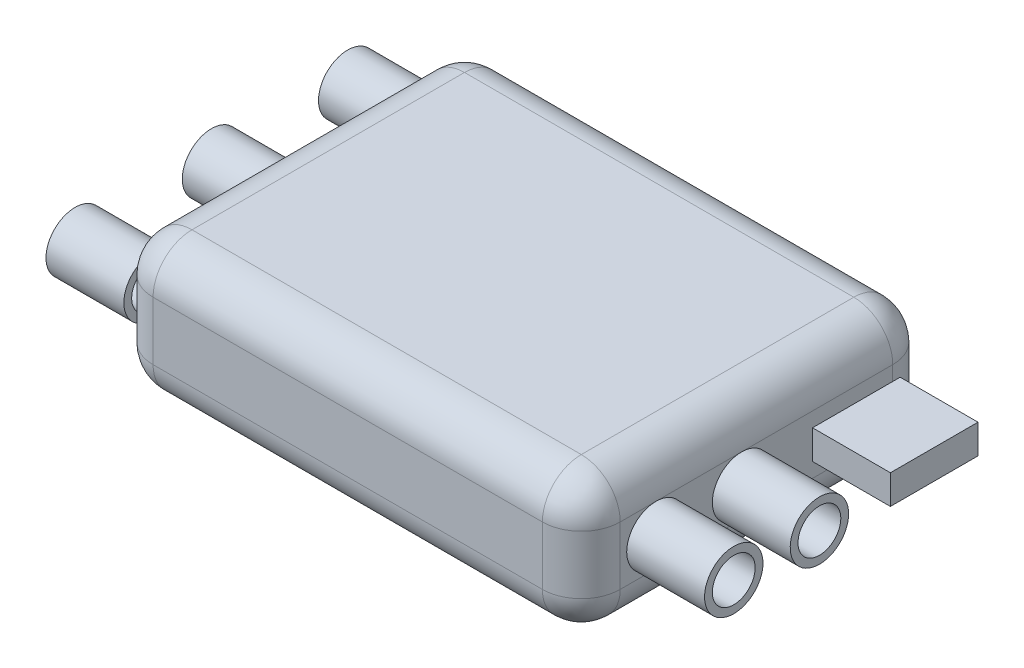
SolidWorks part; units mm, degrees
ref_plane "Front Plane" through (0, 0, 0) normal (0, 0, 1) x (1, 0, 0)
ref_plane "Top Plane" through (0, 0, 0) normal (0, 1, 0) x (1, 0, 0)
ref_plane "Right Plane" through (0, 0, 0) normal (1, 0, 0) x (0, 0, -1)
sketch "Sketch1" plane through (0, 0, 0) normal (0, 1, 0) x (1, 0, 0)
  line L1 (-10, -9) -> (10, -9)
  line L2 (-12, -7) -> (-12, 7)
  line L3 (-10, 9) -> (10, 9)
  line L4 (12, -7) -> (12, 7)
  line L5 (-12, -9) -> (12, 9) construction
  line L6 (-12, 9) -> (12, -9) construction
  arc A0 (-10, -9) -> (-12, -7) centre (-10, -7) cw
  arc A1 (10, -9) -> (12, -7) centre (10, -7) ccw
  arc A2 (10, 9) -> (12, 7) centre (10, 7) cw
  arc A3 (-12, 7) -> (-10, 9) centre (-10, 7) cw
  point P0 (0, 0)
  dimension "D3" = 2
  dimension "D1" = 24
  dimension "D2" = 18
extrude "Boss-Extrude1" add sketch "Sketch1" along normal blind 7
fillet "Fillet1" radius 2 16 edges at (0, 0, 9) (11.4142, 0, 8.4142) (12, 0, 0) (11.4142, 0, -8.4142) (0, 0, -9) (-11.4142, 0, -8.4142) (-12, 0, 0) (-11.4142, 0, 8.4142) (-12, 7, 0) (-11.4142, 7, -8.4142) (0, 7, -9) (11.4142, 7, -8.4142) (12, 7, 0) (11.4142, 7, 8.4142) (0, 7, 9) (-11.4142, 7, 8.4142)
sketch "Sketch2" plane through (-12, 0, 0) normal (-1, 0, 0) x (0, 0, 1)
  line L0 (-7, 3.5) -> (7, 3.5) construction
  line L1 (-7, 5) -> (-7, 2) construction
  line L2 (7, 5) -> (7, 2) construction
  circle A0 centre (-7, 3.5) radius 1.5
  circle A1 centre (0, 3.5) radius 1.5
  circle A2 centre (7, 3.5) radius 1.5
  circle A3 centre (-7, 3.5) radius 1.1
  circle A4 centre (0, 3.5) radius 1.1
  circle A5 centre (7, 3.5) radius 1.1
  dimension "D1" = 0.4
extrude "Boss-Extrude2" add sketch "Sketch2" along normal blind 4
sketch "Sketch3" plane through (12, 0, 0) normal (1, 0, 0) x (0, 0, -1)
  line L0 (-7, 3.5) -> (7, 3.5) construction
  line L1 (-7, 5) -> (-7, 2) construction
  line L2 (7, 5) -> (7, 2) construction
  line L8 (2.8798, 4.25) -> (7.3798, 4.25)
  line L9 (2.8798, 4.25) -> (2.8798, 2.75)
  line L10 (2.8798, 2.75) -> (7.3798, 2.75)
  line L11 (7.3798, 4.25) -> (7.3798, 2.75)
  circle A0 centre (-5.1675, 3.5) radius 1.5
  circle A1 centre (-0.7675, 3.5) radius 1.5
  circle A2 centre (-5.1675, 3.5) radius 1.1
  circle A3 centre (-0.7675, 3.5) radius 1.1
  dimension "D3" = 3
  dimension "D4" = 0.4
  dimension "D1" = 4.5
  dimension "D2" = 1.5
  dimension "D5" = 4.4
extrude "Boss-Extrude3" add sketch "Sketch3" along normal blind 4
